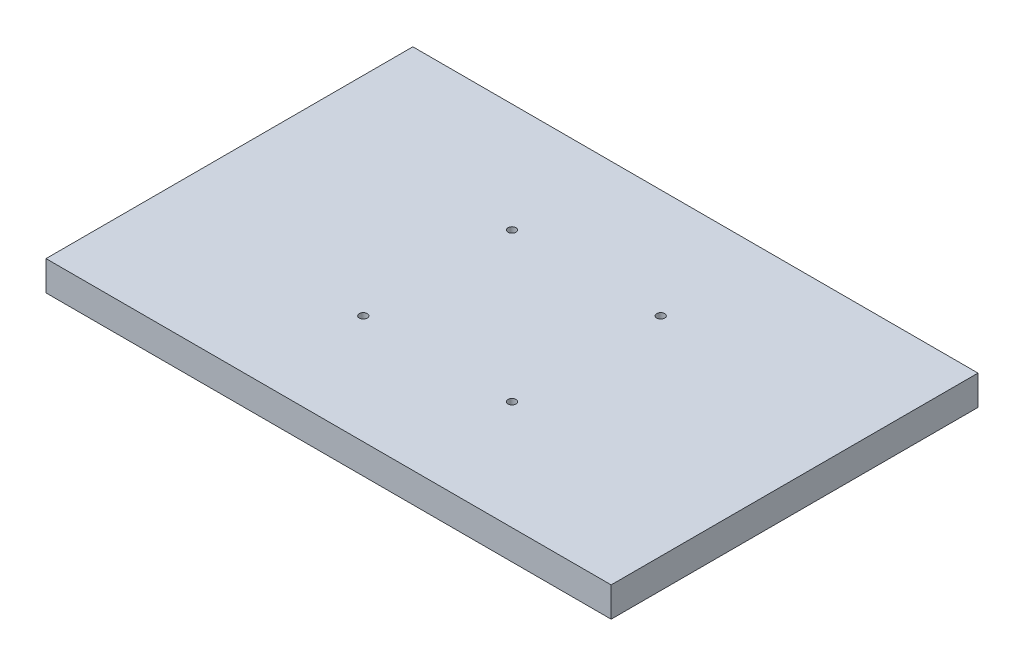
SolidWorks part; units mm, degrees
ref_plane "前视基准面" through (0, 0, 0) normal (0, 0, 1) x (1, 0, 0)
ref_plane "上视基准面" through (0, 0, 0) normal (0, 1, 0) x (1, 0, 0)
ref_plane "右视基准面" through (0, 0, 0) normal (1, 0, 0) x (0, 0, -1)
sketch "草图1" plane through (0, 0, 0) normal (0, 1, 0) x (1, 0, 0)
  line L1 (-142.5, 92.5) -> (142.5, 92.5)
  line L2 (-142.5, 92.5) -> (-142.5, -92.5)
  line L3 (-142.5, -92.5) -> (142.5, -92.5)
  line L4 (142.5, 92.5) -> (142.5, -92.5)
  line L5 (-142.5, 92.5) -> (142.5, -92.5) construction
  line L6 (-142.5, -92.5) -> (142.5, 92.5) construction
  point P0 (0, 0)
  dimension "D1" = 285
  dimension "D2" = 185
extrude "凸台-拉伸1" add sketch "草图1" along normal blind 14
sketch "草图2" plane through (0, 14, 0) normal (0, 1, 0) x (1, 0, 0)
  line L0 (0, 0) -> (175.3266, 0) construction
  line L1 (0, 0) -> (0, 110.944) construction
  circle A0 centre (-37.5, 37.5) radius 2
  circle A1 centre (37.5, 37.5) radius 2
  circle A2 centre (37.5, -37.5) radius 2
  circle A3 centre (-37.5, -37.5) radius 2
  dimension "D1" = 4
  dimension "D2" = 75
  dimension "D3" = 75
extrude "切除-拉伸1" cut sketch "草图2" against normal blind 8
sketch "草图3" plane through (0, 0, 0) normal (0, -1, 0) x (1, 0, 0)
  line L0 (142.5, 92.5) -> (142.5, -92.5) construction
  line L1 (-142.5, -92.5) -> (142.5, -92.5)
  line L2 (-142.5, -92.5) -> (-142.5, -68.5)
  line L3 (-137.5, -68.5) -> (137.5, -68.5)
  line L4 (142.5, -92.5) -> (142.5, -68.5)
  line L6 (142.5, 92.5) -> (137.5, 92.5)
  line L7 (142.5, 92.5) -> (142.5, -68.5)
  line L9 (137.5, 87.5) -> (137.5, -68.5)
  line L10 (-142.5, 92.5) -> (-137.5, 92.5)
  line L11 (-142.5, 92.5) -> (-142.5, -68.5)
  line L13 (-137.5, 87.5) -> (-137.5, -68.5)
  line L14 (-137.5, 92.5) -> (137.5, 92.5)
  line L16 (-137.5, 87.5) -> (137.5, 87.5)
  dimension "D1" = 24
  dimension "D2" = 5
  dimension "D3" = 5
  dimension "D4" = 5
extrude "凸台-拉伸2" add sketch "草图3" along normal blind 1
